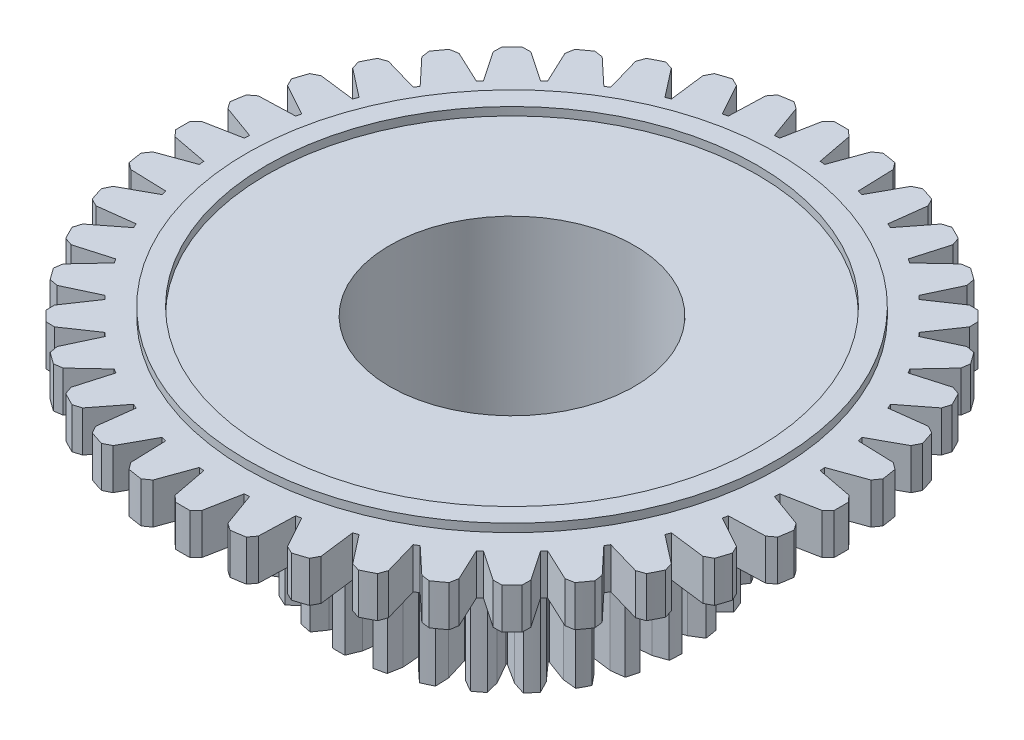
SolidWorks part; units mm, degrees
ref_plane "Front Plane" through (0, 0, 0) normal (0, 0, 1) x (1, 0, 0)
ref_plane "Top Plane" through (0, 0, 0) normal (0, 1, 0) x (1, 0, 0)
ref_plane "Right Plane" through (0, 0, 0) normal (1, 0, 0) x (0, 0, -1)
sketch "Sketch1" plane through (0, 0, 0) normal (0, 1, 0) x (1, 0, 0)
  line L0 (0, 0) -> (0, 8.07) construction
  line L1 (0, 0) -> (0.4932, 7.0528) construction
  line L2 (-0.1762, 8.0681) -> (-0.3262, 7.9225)
  line L3 (0.1762, 8.0681) -> (0.3262, 7.9225)
  line L4 (0.3262, 7.9225) -> (0.4932, 7.0528)
  line L5 (-0.3262, 7.9225) -> (-0.4932, 7.0528)
  line L6 (1.0881, 7.9963) -> (0.9171, 7.876)
  line L7 (1.4362, 7.9412) -> (1.5616, 7.7739)
  line L8 (1.5616, 7.7739) -> (1.5904, 6.8888)
  line L9 (0.9171, 7.876) -> (0.6162, 7.0431)
  line L10 (2.3256, 7.7277) -> (2.1379, 7.6355)
  line L11 (2.6608, 7.6187) -> (2.7585, 7.4339)
  line L12 (2.7585, 7.4339) -> (2.6485, 6.5552)
  line L13 (2.1379, 7.6355) -> (1.7104, 6.86)
  line L14 (3.5058, 7.2687) -> (3.306, 7.2071)
  line L15 (3.8199, 7.1087) -> (3.8874, 6.9109)
  line L16 (3.8874, 6.9109) -> (3.6413, 6.0602)
  line L17 (3.306, 7.2071) -> (2.7625, 6.508)
  line L18 (4.5997, 6.6308) -> (4.3928, 6.6012)
  line L19 (4.8849, 6.4236) -> (4.9207, 6.2177)
  line L20 (4.9207, 6.2177) -> (4.5445, 5.4159)
  line L21 (4.3928, 6.6012) -> (3.7465, 5.9957)
  line L22 (5.5804, 5.8296) -> (5.3714, 5.8327)
  line L23 (5.8296, 5.5804) -> (5.8327, 5.3714)
  line L24 (5.8327, 5.3714) -> (5.3358, 4.6383)
  line L25 (5.3714, 5.8327) -> (4.6383, 5.3358)
  line L26 (6.4236, 4.8849) -> (6.2177, 4.9207)
  line L27 (6.6308, 4.5997) -> (6.6012, 4.3928)
  line L28 (6.6012, 4.3928) -> (5.9957, 3.7465)
  line L29 (6.2177, 4.9207) -> (5.4159, 4.5445)
  line L30 (7.1087, 3.8199) -> (6.9109, 3.8874)
  line L31 (7.2687, 3.5058) -> (7.2071, 3.306)
  line L32 (7.2071, 3.306) -> (6.508, 2.7625)
  line L33 (6.9109, 3.8874) -> (6.0602, 3.6413)
  line L34 (7.6187, 2.6608) -> (7.4339, 2.7585)
  line L35 (7.7277, 2.3256) -> (7.6355, 2.1379)
  line L36 (7.6355, 2.1379) -> (6.86, 1.7104)
  line L37 (7.4339, 2.7585) -> (6.5552, 2.6485)
  line L38 (7.9412, 1.4362) -> (7.7739, 1.5616)
  line L39 (7.9963, 1.0881) -> (7.876, 0.9171)
  line L40 (7.876, 0.9171) -> (7.0431, 0.6162)
  line L41 (7.7739, 1.5616) -> (6.8888, 1.5904)
  line L42 (8.0681, 0.1762) -> (7.9225, 0.3262)
  line L43 (8.0681, -0.1762) -> (7.9225, -0.3262)
  line L44 (7.9225, -0.3262) -> (7.0528, -0.4932)
  line L45 (7.9225, 0.3262) -> (7.0528, 0.4932)
  line L46 (7.9963, -1.0881) -> (7.876, -0.9171)
  line L47 (7.9412, -1.4362) -> (7.7739, -1.5616)
  line L48 (7.7739, -1.5616) -> (6.8888, -1.5904)
  line L49 (7.876, -0.9171) -> (7.0431, -0.6162)
  line L50 (7.7277, -2.3256) -> (7.6355, -2.1379)
  line L51 (7.6187, -2.6608) -> (7.4339, -2.7585)
  line L52 (7.4339, -2.7585) -> (6.5552, -2.6485)
  line L53 (7.6355, -2.1379) -> (6.86, -1.7104)
  line L54 (7.2687, -3.5058) -> (7.2071, -3.306)
  line L55 (7.1087, -3.8199) -> (6.9109, -3.8874)
  line L56 (6.9109, -3.8874) -> (6.0602, -3.6413)
  line L57 (7.2071, -3.306) -> (6.508, -2.7625)
  line L58 (6.6308, -4.5997) -> (6.6012, -4.3928)
  line L59 (6.4236, -4.8849) -> (6.2177, -4.9207)
  line L60 (6.2177, -4.9207) -> (5.4159, -4.5445)
  line L61 (6.6012, -4.3928) -> (5.9957, -3.7465)
  line L62 (5.8296, -5.5804) -> (5.8327, -5.3714)
  line L63 (5.5804, -5.8296) -> (5.3714, -5.8327)
  line L64 (5.3714, -5.8327) -> (4.6383, -5.3358)
  line L65 (5.8327, -5.3714) -> (5.3358, -4.6383)
  line L66 (4.8849, -6.4236) -> (4.9207, -6.2177)
  line L67 (4.5997, -6.6308) -> (4.3928, -6.6012)
  line L68 (4.3928, -6.6012) -> (3.7465, -5.9957)
  line L69 (4.9207, -6.2177) -> (4.5445, -5.4159)
  line L70 (3.8199, -7.1087) -> (3.8874, -6.9109)
  line L71 (3.5058, -7.2687) -> (3.306, -7.2071)
  line L72 (3.306, -7.2071) -> (2.7625, -6.508)
  line L73 (3.8874, -6.9109) -> (3.6413, -6.0602)
  line L74 (2.6608, -7.6187) -> (2.7585, -7.4339)
  line L75 (2.3256, -7.7277) -> (2.1379, -7.6355)
  line L76 (2.1379, -7.6355) -> (1.7104, -6.86)
  line L77 (2.7585, -7.4339) -> (2.6485, -6.5552)
  line L78 (1.4362, -7.9412) -> (1.5616, -7.7739)
  line L79 (1.0881, -7.9963) -> (0.9171, -7.876)
  line L80 (0.9171, -7.876) -> (0.6162, -7.0431)
  line L81 (1.5616, -7.7739) -> (1.5904, -6.8888)
  line L82 (0.1762, -8.0681) -> (0.3262, -7.9225)
  line L83 (-0.1762, -8.0681) -> (-0.3262, -7.9225)
  line L84 (-0.3262, -7.9225) -> (-0.4932, -7.0528)
  line L85 (0.3262, -7.9225) -> (0.4932, -7.0528)
  line L86 (-1.0881, -7.9963) -> (-0.9171, -7.876)
  line L87 (-1.4362, -7.9412) -> (-1.5616, -7.7739)
  line L88 (-1.5616, -7.7739) -> (-1.5904, -6.8888)
  line L89 (-0.9171, -7.876) -> (-0.6162, -7.0431)
  line L90 (-2.3256, -7.7277) -> (-2.1379, -7.6355)
  line L91 (-2.6608, -7.6187) -> (-2.7585, -7.4339)
  line L92 (-2.7585, -7.4339) -> (-2.6485, -6.5552)
  line L93 (-2.1379, -7.6355) -> (-1.7104, -6.86)
  line L94 (-3.5058, -7.2687) -> (-3.306, -7.2071)
  line L95 (-3.8199, -7.1087) -> (-3.8874, -6.9109)
  line L96 (-3.8874, -6.9109) -> (-3.6413, -6.0602)
  line L97 (-3.306, -7.2071) -> (-2.7625, -6.508)
  line L98 (-4.5997, -6.6308) -> (-4.3928, -6.6012)
  line L99 (-4.8849, -6.4236) -> (-4.9207, -6.2177)
  line L100 (-4.9207, -6.2177) -> (-4.5445, -5.4159)
  line L101 (-4.3928, -6.6012) -> (-3.7465, -5.9957)
  line L102 (-5.5804, -5.8296) -> (-5.3714, -5.8327)
  line L103 (-5.8296, -5.5804) -> (-5.8327, -5.3714)
  line L104 (-5.8327, -5.3714) -> (-5.3358, -4.6383)
  line L105 (-5.3714, -5.8327) -> (-4.6383, -5.3358)
  line L106 (-6.4236, -4.8849) -> (-6.2177, -4.9207)
  line L107 (-6.6308, -4.5997) -> (-6.6012, -4.3928)
  line L108 (-6.6012, -4.3928) -> (-5.9957, -3.7465)
  line L109 (-6.2177, -4.9207) -> (-5.4159, -4.5445)
  line L110 (-7.1087, -3.8199) -> (-6.9109, -3.8874)
  line L111 (-7.2687, -3.5058) -> (-7.2071, -3.306)
  line L112 (-7.2071, -3.306) -> (-6.508, -2.7625)
  line L113 (-6.9109, -3.8874) -> (-6.0602, -3.6413)
  line L114 (-7.6187, -2.6608) -> (-7.4339, -2.7585)
  line L115 (-7.7277, -2.3256) -> (-7.6355, -2.1379)
  line L116 (-7.6355, -2.1379) -> (-6.86, -1.7104)
  line L117 (-7.4339, -2.7585) -> (-6.5552, -2.6485)
  line L118 (-7.9412, -1.4362) -> (-7.7739, -1.5616)
  line L119 (-7.9963, -1.0881) -> (-7.876, -0.9171)
  line L120 (-7.876, -0.9171) -> (-7.0431, -0.6162)
  line L121 (-7.7739, -1.5616) -> (-6.8888, -1.5904)
  line L122 (-8.0681, -0.1762) -> (-7.9225, -0.3262)
  line L123 (-8.0681, 0.1762) -> (-7.9225, 0.3262)
  line L124 (-7.9225, 0.3262) -> (-7.0528, 0.4932)
  line L125 (-7.9225, -0.3262) -> (-7.0528, -0.4932)
  line L126 (-7.9963, 1.0881) -> (-7.876, 0.9171)
  line L127 (-7.9412, 1.4362) -> (-7.7739, 1.5616)
  line L128 (-7.7739, 1.5616) -> (-6.8888, 1.5904)
  line L129 (-7.876, 0.9171) -> (-7.0431, 0.6162)
  line L130 (-7.7277, 2.3256) -> (-7.6355, 2.1379)
  line L131 (-7.6187, 2.6608) -> (-7.4339, 2.7585)
  line L132 (-7.4339, 2.7585) -> (-6.5552, 2.6485)
  line L133 (-7.6355, 2.1379) -> (-6.86, 1.7104)
  line L134 (-7.2687, 3.5058) -> (-7.2071, 3.306)
  line L135 (-7.1087, 3.8199) -> (-6.9109, 3.8874)
  line L136 (-6.9109, 3.8874) -> (-6.0602, 3.6413)
  line L137 (-7.2071, 3.306) -> (-6.508, 2.7625)
  line L138 (-6.6308, 4.5997) -> (-6.6012, 4.3928)
  line L139 (-6.4236, 4.8849) -> (-6.2177, 4.9207)
  line L140 (-6.2177, 4.9207) -> (-5.4159, 4.5445)
  line L141 (-6.6012, 4.3928) -> (-5.9957, 3.7465)
  line L142 (-5.8296, 5.5804) -> (-5.8327, 5.3714)
  line L143 (-5.5804, 5.8296) -> (-5.3714, 5.8327)
  line L144 (-5.3714, 5.8327) -> (-4.6383, 5.3358)
  line L145 (-5.8327, 5.3714) -> (-5.3358, 4.6383)
  line L146 (-4.8849, 6.4236) -> (-4.9207, 6.2177)
  line L147 (-4.5997, 6.6308) -> (-4.3928, 6.6012)
  line L148 (-4.3928, 6.6012) -> (-3.7465, 5.9957)
  line L149 (-4.9207, 6.2177) -> (-4.5445, 5.4159)
  line L150 (-3.8199, 7.1087) -> (-3.8874, 6.9109)
  line L151 (-3.5058, 7.2687) -> (-3.306, 7.2071)
  line L152 (-3.306, 7.2071) -> (-2.7625, 6.508)
  line L153 (-3.8874, 6.9109) -> (-3.6413, 6.0602)
  line L154 (-2.6608, 7.6187) -> (-2.7585, 7.4339)
  line L155 (-2.3256, 7.7277) -> (-2.1379, 7.6355)
  line L156 (-2.1379, 7.6355) -> (-1.7104, 6.86)
  line L157 (-2.7585, 7.4339) -> (-2.6485, 6.5552)
  line L158 (-1.4362, 7.9412) -> (-1.5616, 7.7739)
  line L159 (-1.0881, 7.9963) -> (-0.9171, 7.876)
  line L160 (-0.9171, 7.876) -> (-0.6162, 7.0431)
  line L161 (-1.5616, 7.7739) -> (-1.5904, 6.8888)
  arc A0 (0.1762, 8.0681) -> (-0.1762, 8.0681) centre (0, 0) ccw
  arc A1 (-7.0528, -0.4932) -> (-7.0431, -0.6162) centre (0, 0) ccw
  arc A2 (1.4362, 7.9412) -> (1.0881, 7.9963) centre (0, 0) ccw
  circle A3 centre (0, 0) radius 8.07 construction
  arc A4 (2.6608, 7.6187) -> (2.3256, 7.7277) centre (0, 0) ccw
  arc A5 (3.8199, 7.1087) -> (3.5058, 7.2687) centre (0, 0) ccw
  arc A6 (4.8849, 6.4236) -> (4.5997, 6.6308) centre (0, 0) ccw
  arc A7 (5.8296, 5.5804) -> (5.5804, 5.8296) centre (0, 0) ccw
  arc A8 (6.6308, 4.5997) -> (6.4236, 4.8849) centre (0, 0) ccw
  arc A9 (7.2687, 3.5058) -> (7.1087, 3.8199) centre (0, 0) ccw
  arc A10 (7.7277, 2.3256) -> (7.6187, 2.6608) centre (0, 0) ccw
  arc A11 (7.9963, 1.0881) -> (7.9412, 1.4362) centre (0, 0) ccw
  arc A12 (8.0681, -0.1762) -> (8.0681, 0.1762) centre (0, 0) ccw
  arc A13 (7.9412, -1.4362) -> (7.9963, -1.0881) centre (0, 0) ccw
  arc A14 (7.6187, -2.6608) -> (7.7277, -2.3256) centre (0, 0) ccw
  arc A15 (7.1087, -3.8199) -> (7.2687, -3.5058) centre (0, 0) ccw
  arc A16 (6.4236, -4.8849) -> (6.6308, -4.5997) centre (0, 0) ccw
  arc A17 (5.5804, -5.8296) -> (5.8296, -5.5804) centre (0, 0) ccw
  arc A18 (4.5997, -6.6308) -> (4.8849, -6.4236) centre (0, 0) ccw
  arc A19 (3.5058, -7.2687) -> (3.8199, -7.1087) centre (0, 0) ccw
  arc A20 (2.3256, -7.7277) -> (2.6608, -7.6187) centre (0, 0) ccw
  arc A21 (1.0881, -7.9963) -> (1.4362, -7.9412) centre (0, 0) ccw
  arc A22 (-0.1762, -8.0681) -> (0.1762, -8.0681) centre (0, 0) ccw
  arc A23 (-1.4362, -7.9412) -> (-1.0881, -7.9963) centre (0, 0) ccw
  arc A24 (-2.6608, -7.6187) -> (-2.3256, -7.7277) centre (0, 0) ccw
  arc A25 (-3.8199, -7.1087) -> (-3.5058, -7.2687) centre (0, 0) ccw
  arc A26 (-4.8849, -6.4236) -> (-4.5997, -6.6308) centre (0, 0) ccw
  arc A27 (-5.8296, -5.5804) -> (-5.5804, -5.8296) centre (0, 0) ccw
  arc A28 (-6.6308, -4.5997) -> (-6.4236, -4.8849) centre (0, 0) ccw
  arc A29 (-7.2687, -3.5058) -> (-7.1087, -3.8199) centre (0, 0) ccw
  arc A30 (-7.7277, -2.3256) -> (-7.6187, -2.6608) centre (0, 0) ccw
  arc A31 (-7.9963, -1.0881) -> (-7.9412, -1.4362) centre (0, 0) ccw
  arc A32 (-8.0681, 0.1762) -> (-8.0681, -0.1762) centre (0, 0) ccw
  arc A33 (-7.9412, 1.4362) -> (-7.9963, 1.0881) centre (0, 0) ccw
  arc A34 (-7.6187, 2.6608) -> (-7.7277, 2.3256) centre (0, 0) ccw
  arc A35 (-7.1087, 3.8199) -> (-7.2687, 3.5058) centre (0, 0) ccw
  arc A36 (-6.4236, 4.8849) -> (-6.6308, 4.5997) centre (0, 0) ccw
  arc A37 (-5.5804, 5.8296) -> (-5.8296, 5.5804) centre (0, 0) ccw
  arc A38 (-4.5997, 6.6308) -> (-4.8849, 6.4236) centre (0, 0) ccw
  arc A39 (-3.5058, 7.2687) -> (-3.8199, 7.1087) centre (0, 0) ccw
  arc A40 (-2.3256, 7.7277) -> (-2.6608, 7.6187) centre (0, 0) ccw
  arc A41 (-1.0881, 7.9963) -> (-1.4362, 7.9412) centre (0, 0) ccw
  arc A42 (-7.0431, 0.6162) -> (-7.0528, 0.4932) centre (0, 0) ccw
  circle A43 centre (0, 0) radius 7.07 construction
  arc A44 (-6.86, 1.7104) -> (-6.8888, 1.5904) centre (0, 0) ccw
  arc A45 (-6.508, 2.7625) -> (-6.5552, 2.6485) centre (0, 0) ccw
  arc A46 (-5.9957, 3.7465) -> (-6.0602, 3.6413) centre (0, 0) ccw
  arc A47 (-5.3358, 4.6383) -> (-5.4159, 4.5445) centre (0, 0) ccw
  arc A48 (-4.5445, 5.4159) -> (-4.6383, 5.3358) centre (0, 0) ccw
  arc A49 (-3.6413, 6.0602) -> (-3.7465, 5.9957) centre (0, 0) ccw
  arc A50 (-2.6485, 6.5552) -> (-2.7625, 6.508) centre (0, 0) ccw
  arc A51 (-1.5904, 6.8888) -> (-1.7104, 6.86) centre (0, 0) ccw
  arc A52 (-0.4932, 7.0528) -> (-0.6162, 7.0431) centre (0, 0) ccw
  arc A53 (0.6162, 7.0431) -> (0.4932, 7.0528) centre (0, 0) ccw
  arc A54 (1.7104, 6.86) -> (1.5904, 6.8888) centre (0, 0) ccw
  arc A55 (2.7625, 6.508) -> (2.6485, 6.5552) centre (0, 0) ccw
  arc A56 (3.7465, 5.9957) -> (3.6413, 6.0602) centre (0, 0) ccw
  arc A57 (4.6383, 5.3358) -> (4.5445, 5.4159) centre (0, 0) ccw
  arc A58 (5.4159, 4.5445) -> (5.3358, 4.6383) centre (0, 0) ccw
  arc A59 (6.0602, 3.6413) -> (5.9957, 3.7465) centre (0, 0) ccw
  arc A60 (6.5552, 2.6485) -> (6.508, 2.7625) centre (0, 0) ccw
  arc A61 (6.8888, 1.5904) -> (6.86, 1.7104) centre (0, 0) ccw
  arc A62 (7.0528, 0.4932) -> (7.0431, 0.6162) centre (0, 0) ccw
  arc A63 (-6.8888, -1.5904) -> (-6.86, -1.7104) centre (0, 0) ccw
  arc A64 (-6.5552, -2.6485) -> (-6.508, -2.7625) centre (0, 0) ccw
  arc A65 (-6.0602, -3.6413) -> (-5.9957, -3.7465) centre (0, 0) ccw
  arc A66 (-5.4159, -4.5445) -> (-5.3358, -4.6383) centre (0, 0) ccw
  arc A67 (-4.6383, -5.3358) -> (-4.5445, -5.4159) centre (0, 0) ccw
  arc A68 (-3.7465, -5.9957) -> (-3.6413, -6.0602) centre (0, 0) ccw
  arc A69 (-2.7625, -6.508) -> (-2.6485, -6.5552) centre (0, 0) ccw
  arc A70 (-1.7104, -6.86) -> (-1.5904, -6.8888) centre (0, 0) ccw
  arc A71 (-0.6162, -7.0431) -> (-0.4932, -7.0528) centre (0, 0) ccw
  arc A72 (0.4932, -7.0528) -> (0.6162, -7.0431) centre (0, 0) ccw
  arc A73 (1.5904, -6.8888) -> (1.7104, -6.86) centre (0, 0) ccw
  arc A74 (2.6485, -6.5552) -> (2.7625, -6.508) centre (0, 0) ccw
  arc A75 (3.6413, -6.0602) -> (3.7465, -5.9957) centre (0, 0) ccw
  arc A76 (4.5445, -5.4159) -> (4.6383, -5.3358) centre (0, 0) ccw
  arc A77 (5.3358, -4.6383) -> (5.4159, -4.5445) centre (0, 0) ccw
  arc A78 (5.9957, -3.7465) -> (6.0602, -3.6413) centre (0, 0) ccw
  arc A79 (6.508, -2.7625) -> (6.5552, -2.6485) centre (0, 0) ccw
  arc A80 (6.86, -1.7104) -> (6.8888, -1.5904) centre (0, 0) ccw
  arc A81 (7.0431, -0.6162) -> (7.0528, -0.4932) centre (0, 0) ccw
  point P5 (7.7174, 2.3594)
  point P7 (6.7611, 2.0671)
  point P250 (0, 0)
  dimension "D1" = 16.14
  dimension "D3" = 14.14
  dimension "D5" = 0.15
  dimension "D4" = 4
  dimension "D2" = 1
  dimension "D6" = 40
extrude "Boss-Extrude1" add sketch "Sketch1" along normal blind 1
sketch "Sketch2" plane through (0, 1, 0) normal (0, 1, 0) x (1, 0, 0)
  circle A0 centre (0, 0) radius 6.5004
  circle A1 centre (0, 0) radius 6.0004
  dimension "D1" = 0.5
extrude "Boss-Extrude2" add sketch "Sketch2" along normal blind 0.2
sketch "Sketch4" plane through (0, 1, 0) normal (0, 1, 0) x (1, 0, 0)
  circle A0 centre (0, 0) radius 2.995
  dimension "D1" = 5.99
extrude "Cut-Extrude3" cut sketch "Sketch4" against normal blind 4.2
sketch "Sketch5" plane through (0, 0, 0) normal (0, 1, 0) x (1, 0, 0)
  circle A0 centre (0, 0) radius 8.07
  circle A1 centre (0, 0) radius 6.5004
sketch "Sketch6" plane through (0, 0, 0) normal (0, -1, 0) x (1, 0, 0)
  line L0 (0, 0) -> (0, 8.2643) construction
  line L1 (0, 0) -> (0.2752, 3.9354) construction
  line L2 (0.1481, 4.2424) -> (0.2752, 3.9354)
  line L3 (0.2752, 3.9354) -> (0.3546, 3.3571)
  line L4 (-0.2752, 3.9354) -> (-0.3546, 3.3571)
  line L5 (-0.1481, 4.2424) -> (-0.2752, 3.9354)
  line L6 (0.5772, 3.9025) -> (0.3754, 3.3549)
  line L7 (0.7673, 4.1751) -> (0.5772, 3.9025)
  line L8 (1.0567, 4.1114) -> (1.1147, 3.7842)
  line L9 (1.1147, 3.7842) -> (1.068, 3.2024)
  line L10 (1.4027, 3.6872) -> (1.0878, 3.1957)
  line L11 (1.6469, 3.9125) -> (1.4027, 3.6872)
  line L12 (1.9158, 3.7881) -> (1.9022, 3.4561)
  line L13 (1.9022, 3.4561) -> (1.7315, 2.898)
  line L14 (2.1625, 3.2995) -> (1.7493, 2.8872)
  line L15 (2.4495, 3.467) -> (2.1625, 3.2995)
  line L16 (2.6853, 3.2877) -> (2.6007, 2.9664)
  line L17 (2.6007, 2.9664) -> (2.314, 2.458)
  line L18 (2.8213, 2.7575) -> (2.3291, 2.4436)
  line L19 (3.1375, 2.8594) -> (2.8213, 2.7575)
  line L20 (3.3293, 2.6336) -> (3.1776, 2.338)
  line L21 (3.1776, 2.338) -> (2.7882, 1.9031)
  line L22 (3.3481, 2.0865) -> (2.8, 1.8858)
  line L23 (3.6788, 2.1181) -> (3.3481, 2.0865)
  line L24 (3.8176, 1.8563) -> (3.6059, 1.6002)
  line L25 (3.6059, 1.6002) -> (3.1322, 1.2592)
  line L26 (3.7183, 1.318) -> (3.1399, 1.2398)
  line L27 (4.0481, 1.2777) -> (3.7183, 1.318)
  line L28 (4.1274, 0.9922) -> (3.8656, 0.7877)
  line L29 (3.8656, 0.7877) -> (3.3296, 0.5564)
  line L30 (3.9147, 0.4878) -> (3.333, 0.5358)
  line L31 (4.2282, 0.3776) -> (3.9147, 0.4878)
  line L32 (4.2442, 0.0817) -> (3.9445, -0.0617)
  line L33 (3.9445, -0.0617) -> (3.3714, -0.1723)
  line L34 (3.9281, -0.3651) -> (3.3703, -0.1932)
  line L35 (4.2105, -0.5401) -> (3.9281, -0.3651)
  line L36 (4.1626, -0.8325) -> (3.839, -0.9082)
  line L37 (3.839, -0.9082) -> (3.2555, -0.8931)
  line L38 (3.7577, -1.201) -> (3.25, -0.9132)
  line L39 (3.9959, -1.4327) -> (3.7577, -1.201)
  line L40 (3.8863, -1.7079) -> (3.554, -1.7123)
  line L41 (3.554, -1.7123) -> (2.9874, -1.572)
  line L42 (3.4117, -1.9807) -> (2.9777, -1.5905)
  line L43 (3.5945, -2.2582) -> (3.4117, -1.9807)
  line L44 (3.4283, -2.5034) -> (3.1028, -2.4363)
  line L45 (3.1028, -2.4363) -> (2.5797, -2.1775)
  line L46 (2.9062, -2.6678) -> (2.5661, -2.1934)
  line L47 (3.0251, -2.9781) -> (2.9062, -2.6678)
  line L48 (2.81, -3.1819) -> (2.5066, -3.0463)
  line L49 (2.5066, -3.0463) -> (2.0513, -2.6811)
  line L50 (2.2647, -3.2302) -> (2.0346, -2.6938)
  line L51 (2.3141, -3.5588) -> (2.2647, -3.2302)
  line L52 (2.0603, -3.7115) -> (1.7931, -3.5139)
  line L53 (1.7931, -3.5139) -> (1.4269, -3.0594)
  line L54 (1.5174, -3.6415) -> (1.408, -3.0682)
  line L55 (1.495, -3.973) -> (1.5174, -3.6415)
  line L56 (1.2142, -4.0676) -> (0.9958, -3.8173)
  line L57 (0.9958, -3.8173) -> (0.7359, -3.2946)
  line L58 (0.6991, -3.8826) -> (0.7155, -3.2991)
  line L59 (0.606, -4.2015) -> (0.6991, -3.8826)
  line L60 (0.3114, -4.2336) -> (0.1519, -3.9421)
  line L61 (0.1519, -3.9421) -> (0.0104, -3.3758)
  line L62 (-0.1519, -3.9421) -> (-0.0104, -3.3758)
  line L63 (-0.3114, -4.2336) -> (-0.1519, -3.9421)
  line L64 (-0.606, -4.2015) -> (-0.6991, -3.8826)
  line L65 (-0.6991, -3.8826) -> (-0.7155, -3.2991)
  line L66 (-0.9958, -3.8173) -> (-0.7359, -3.2946)
  line L67 (-1.2142, -4.0676) -> (-0.9958, -3.8173)
  line L68 (-1.495, -3.973) -> (-1.5174, -3.6415)
  line L69 (-1.5174, -3.6415) -> (-1.408, -3.0682)
  line L70 (-1.7931, -3.5139) -> (-1.4269, -3.0594)
  line L71 (-2.0603, -3.7115) -> (-1.7931, -3.5139)
  line L72 (-2.3141, -3.5588) -> (-2.2647, -3.2302)
  line L73 (-2.2647, -3.2302) -> (-2.0346, -2.6938)
  line L74 (-2.5066, -3.0463) -> (-2.0513, -2.6811)
  line L75 (-2.81, -3.1819) -> (-2.5066, -3.0463)
  line L76 (-3.0251, -2.9781) -> (-2.9062, -2.6678)
  line L77 (-2.9062, -2.6678) -> (-2.5661, -2.1934)
  line L78 (-3.1028, -2.4363) -> (-2.5797, -2.1775)
  line L79 (-3.4283, -2.5034) -> (-3.1028, -2.4363)
  line L80 (-3.5945, -2.2582) -> (-3.4117, -1.9807)
  line L81 (-3.4117, -1.9807) -> (-2.9777, -1.5905)
  line L82 (-3.554, -1.7123) -> (-2.9874, -1.572)
  line L83 (-3.8863, -1.7079) -> (-3.554, -1.7123)
  line L84 (-3.9959, -1.4327) -> (-3.7577, -1.201)
  line L85 (-3.7577, -1.201) -> (-3.25, -0.9132)
  line L86 (-3.839, -0.9082) -> (-3.2555, -0.8931)
  line L87 (-4.1626, -0.8325) -> (-3.839, -0.9082)
  line L88 (-4.2105, -0.5401) -> (-3.9281, -0.3651)
  line L89 (-3.9281, -0.3651) -> (-3.3703, -0.1932)
  line L90 (-3.9445, -0.0617) -> (-3.3714, -0.1723)
  line L91 (-4.2442, 0.0817) -> (-3.9445, -0.0617)
  line L92 (-4.2282, 0.3776) -> (-3.9147, 0.4878)
  line L93 (-3.9147, 0.4878) -> (-3.333, 0.5358)
  line L94 (-3.8656, 0.7877) -> (-3.3296, 0.5564)
  line L95 (-4.1274, 0.9922) -> (-3.8656, 0.7877)
  line L96 (-4.0481, 1.2777) -> (-3.7183, 1.318)
  line L97 (-3.7183, 1.318) -> (-3.1399, 1.2398)
  line L98 (-3.6059, 1.6002) -> (-3.1322, 1.2592)
  line L99 (-3.8176, 1.8563) -> (-3.6059, 1.6002)
  line L100 (-3.6788, 2.1181) -> (-3.3481, 2.0865)
  line L101 (-3.3481, 2.0865) -> (-2.8, 1.8858)
  line L102 (-3.1776, 2.338) -> (-2.7882, 1.9031)
  line L103 (-3.3293, 2.6336) -> (-3.1776, 2.338)
  line L104 (-3.1375, 2.8594) -> (-2.8213, 2.7575)
  line L105 (-2.8213, 2.7575) -> (-2.3291, 2.4436)
  line L106 (-2.6007, 2.9664) -> (-2.314, 2.458)
  line L107 (-2.6853, 3.2877) -> (-2.6007, 2.9664)
  line L108 (-2.4495, 3.467) -> (-2.1625, 3.2995)
  line L109 (-2.1625, 3.2995) -> (-1.7493, 2.8872)
  line L110 (-1.9022, 3.4561) -> (-1.7315, 2.898)
  line L111 (-1.9158, 3.7881) -> (-1.9022, 3.4561)
  line L112 (-1.6469, 3.9125) -> (-1.4027, 3.6872)
  line L113 (-1.4027, 3.6872) -> (-1.0878, 3.1957)
  line L114 (-1.1147, 3.7842) -> (-1.068, 3.2024)
  line L115 (-1.0567, 4.1114) -> (-1.1147, 3.7842)
  line L116 (-0.7673, 4.1751) -> (-0.5772, 3.9025)
  line L117 (-0.5772, 3.9025) -> (-0.3754, 3.3549)
  arc A0 (0.1481, 4.2424) -> (-0.1481, 4.2424) centre (0, 0) ccw
  circle A1 centre (0, 0) radius 2.995 construction
  circle A2 centre (0, 0) radius 2.995
  circle A3 centre (0, 0) radius 3.945 construction
  arc A4 (-1.068, 3.2024) -> (-1.0878, 3.1957) centre (0, 0) ccw
  circle A5 centre (0, 0) radius 4.245 construction
  arc A6 (1.0567, 4.1114) -> (0.7673, 4.1751) centre (0, 0) ccw
  arc A7 (1.9158, 3.7881) -> (1.6469, 3.9125) centre (0, 0) ccw
  arc A8 (2.6853, 3.2877) -> (2.4495, 3.467) centre (0, 0) ccw
  arc A9 (3.3293, 2.6336) -> (3.1375, 2.8594) centre (0, 0) ccw
  arc A10 (3.8176, 1.8563) -> (3.6788, 2.1181) centre (0, 0) ccw
  arc A11 (4.1274, 0.9922) -> (4.0481, 1.2777) centre (0, 0) ccw
  arc A12 (4.2442, 0.0817) -> (4.2282, 0.3776) centre (0, 0) ccw
  arc A13 (4.1626, -0.8325) -> (4.2105, -0.5401) centre (0, 0) ccw
  arc A14 (3.8863, -1.7079) -> (3.9959, -1.4327) centre (0, 0) ccw
  arc A15 (3.4283, -2.5034) -> (3.5945, -2.2582) centre (0, 0) ccw
  arc A16 (2.81, -3.1819) -> (3.0251, -2.9781) centre (0, 0) ccw
  arc A17 (2.0603, -3.7115) -> (2.3141, -3.5588) centre (0, 0) ccw
  arc A18 (1.2142, -4.0676) -> (1.495, -3.973) centre (0, 0) ccw
  arc A19 (0.3114, -4.2336) -> (0.606, -4.2015) centre (0, 0) ccw
  arc A20 (-0.606, -4.2015) -> (-0.3114, -4.2336) centre (0, 0) ccw
  arc A21 (-1.495, -3.973) -> (-1.2142, -4.0676) centre (0, 0) ccw
  arc A22 (-2.3141, -3.5588) -> (-2.0603, -3.7115) centre (0, 0) ccw
  arc A23 (-3.0251, -2.9781) -> (-2.81, -3.1819) centre (0, 0) ccw
  arc A24 (-3.5945, -2.2582) -> (-3.4283, -2.5034) centre (0, 0) ccw
  arc A25 (-3.9959, -1.4327) -> (-3.8863, -1.7079) centre (0, 0) ccw
  arc A26 (-4.2105, -0.5401) -> (-4.1626, -0.8325) centre (0, 0) ccw
  arc A27 (-4.2282, 0.3776) -> (-4.2442, 0.0817) centre (0, 0) ccw
  arc A28 (-4.0481, 1.2777) -> (-4.1274, 0.9922) centre (0, 0) ccw
  arc A29 (-3.6788, 2.1181) -> (-3.8176, 1.8563) centre (0, 0) ccw
  arc A30 (-3.1375, 2.8594) -> (-3.3293, 2.6336) centre (0, 0) ccw
  arc A31 (-2.4495, 3.467) -> (-2.6853, 3.2877) centre (0, 0) ccw
  arc A32 (-1.6469, 3.9125) -> (-1.9158, 3.7881) centre (0, 0) ccw
  arc A33 (-0.7673, 4.1751) -> (-1.0567, 4.1114) centre (0, 0) ccw
  arc A34 (-1.7315, 2.898) -> (-1.7493, 2.8872) centre (0, 0) ccw
  arc A35 (-2.314, 2.458) -> (-2.3291, 2.4436) centre (0, 0) ccw
  arc A36 (-2.7882, 1.9031) -> (-2.8, 1.8858) centre (0, 0) ccw
  arc A37 (-3.1322, 1.2592) -> (-3.1399, 1.2398) centre (0, 0) ccw
  arc A38 (-3.3296, 0.5564) -> (-3.333, 0.5358) centre (0, 0) ccw
  arc A39 (-3.3714, -0.1723) -> (-3.3703, -0.1932) centre (0, 0) ccw
  arc A40 (-3.2555, -0.8931) -> (-3.25, -0.9132) centre (0, 0) ccw
  arc A41 (-2.9874, -1.572) -> (-2.9777, -1.5905) centre (0, 0) ccw
  arc A42 (-2.5797, -2.1775) -> (-2.5661, -2.1934) centre (0, 0) ccw
  arc A43 (-2.0513, -2.6811) -> (-2.0346, -2.6938) centre (0, 0) ccw
  arc A44 (-1.4269, -3.0594) -> (-1.408, -3.0682) centre (0, 0) ccw
  arc A45 (-0.7359, -3.2946) -> (-0.7155, -3.2991) centre (0, 0) ccw
  arc A46 (-0.0104, -3.3758) -> (0.0104, -3.3758) centre (0, 0) ccw
  arc A47 (0.7155, -3.2991) -> (0.7359, -3.2946) centre (0, 0) ccw
  arc A48 (1.408, -3.0682) -> (1.4269, -3.0594) centre (0, 0) ccw
  arc A49 (2.0346, -2.6938) -> (2.0513, -2.6811) centre (0, 0) ccw
  arc A50 (2.5661, -2.1934) -> (2.5797, -2.1775) centre (0, 0) ccw
  arc A51 (2.9777, -1.5905) -> (2.9874, -1.572) centre (0, 0) ccw
  arc A52 (3.25, -0.9132) -> (3.2555, -0.8931) centre (0, 0) ccw
  arc A53 (3.3703, -0.1932) -> (3.3714, -0.1723) centre (0, 0) ccw
  arc A54 (3.333, 0.5358) -> (3.3296, 0.5564) centre (0, 0) ccw
  arc A55 (3.1399, 1.2398) -> (3.1322, 1.2592) centre (0, 0) ccw
  arc A56 (2.8, 1.8858) -> (2.7882, 1.9031) centre (0, 0) ccw
  arc A57 (2.3291, 2.4436) -> (2.314, 2.458) centre (0, 0) ccw
  arc A58 (1.7493, 2.8872) -> (1.7315, 2.898) centre (0, 0) ccw
  arc A59 (1.0878, 3.1957) -> (1.068, 3.2024) centre (0, 0) ccw
  arc A60 (0.3754, 3.3549) -> (0.3546, 3.3571) centre (0, 0) ccw
  arc A61 (-0.3546, 3.3571) -> (-0.3754, 3.3549) centre (0, 0) ccw
  point P8 (4.0595, 1.2411)
  point P189 (0, 0)
  dimension "D1" = 8.49
  dimension "D3" = 4
  dimension "D2" = 0.3
  dimension "D4" = 29
extrude "Boss-Extrude4" add sketch "Sketch6" along normal blind 4
